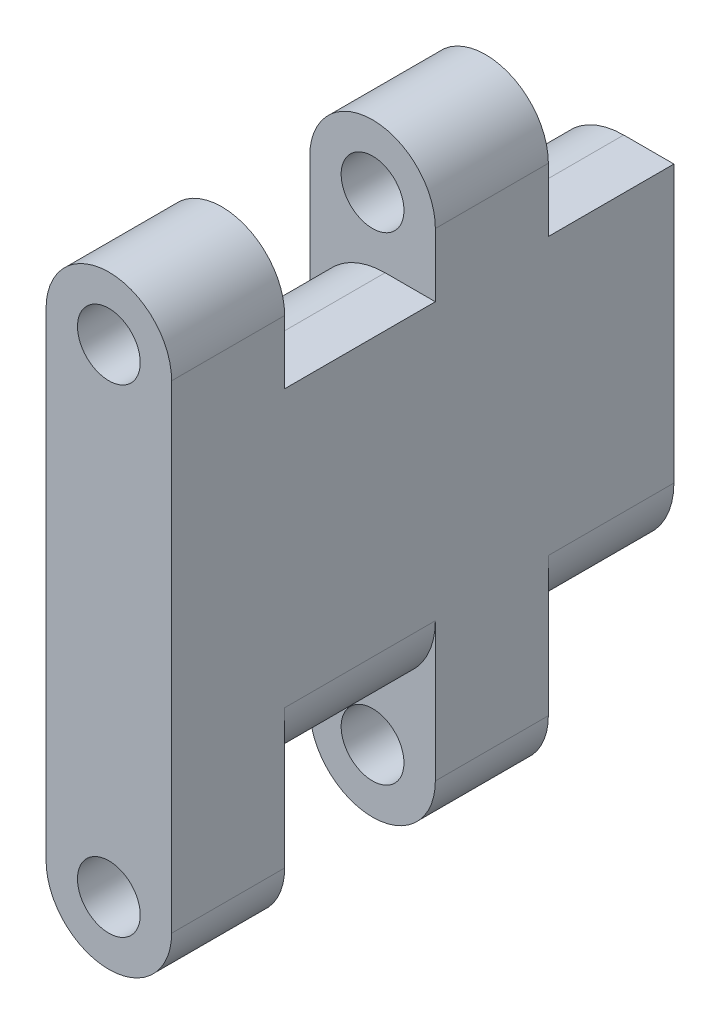
SolidWorks part; units mm, degrees
ref_plane "Front Plane" through (0, 0, 0) normal (0, 0, 1) x (1, 0, 0)
ref_plane "Top Plane" through (0, 0, 0) normal (0, 1, 0) x (1, 0, 0)
ref_plane "Right Plane" through (0, 0, 0) normal (1, 0, 0) x (0, 0, -1)
sketch "Sketch1" plane through (0, 0, 0) normal (1, 0, 0) x (0, 0, -1)
  line L1 (-20, 14) -> (20, 14)
  line L2 (-20, 14) -> (-20, -14)
  line L3 (-20, -14) -> (20, -14)
  line L4 (20, 14) -> (20, -14)
  line L5 (-20, 14) -> (20, -14) construction
  line L6 (-20, -14) -> (20, 14) construction
  point P0 (0, 0)
  dimension "D1" = 40
  dimension "D2" = 28
extrude "Boss-Extrude1" add sketch "Sketch1" along normal blind 10
sketch "Sketch2" plane through (0, 0, 20) normal (0, 0, 1) x (1, 0, 0)
  line L0 (5, 14) -> (5, -14) construction
  line L1 (10, 14) -> (0, 14) construction
  line L2 (10, -14) -> (0, -14) construction
  line L3 (5, 19.05) -> (5, -19.05) construction
  line L4 (10, 19.05) -> (10, -19.05)
  line L5 (0, 19.05) -> (0, -19.05)
  arc A0 (10, 19.05) -> (0, 19.05) centre (5, 19.05) ccw
  arc A1 (0, -19.05) -> (10, -19.05) centre (5, -19.05) ccw
  circle A2 centre (5, 19.05) radius 2.5
  circle A3 centre (5, -19.05) radius 2.5
  point P8 (5, 0)
  dimension "D3" = 5
  dimension "D4" = 5
  dimension "D1" = 10
  dimension "D2" = 38.1
extrude "Boss-Extrude2" add sketch "Sketch2" against normal blind 9
pattern_linear "LPattern1" count 2 spacing 21 along (0, 0, -1) of "Boss-Extrude2"
fillet "Fillet1" radius 6 4 edges at (10, -14, -15) (10, -14, 5) (0, 14, -15) (0, 14, 5)
